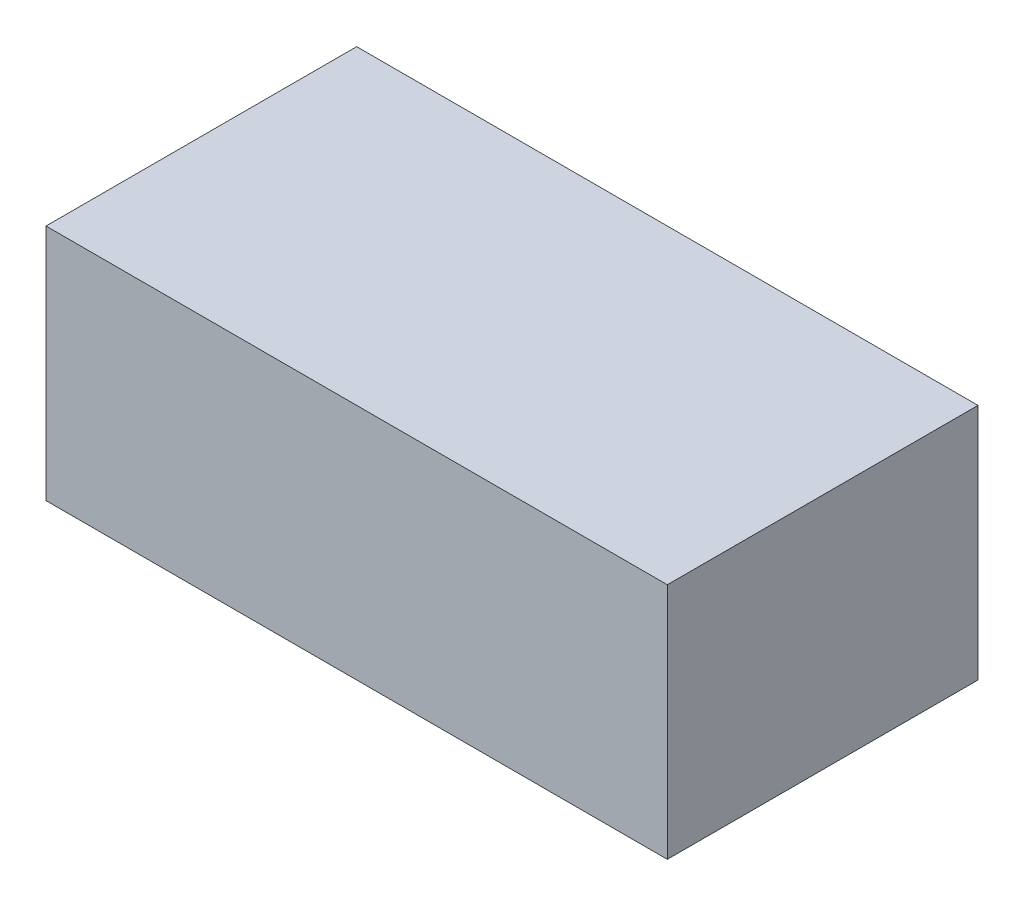
SolidWorks part; units mm, degrees
ref_plane "Front Plane" through (0, 0, 0) normal (0, 0, 1) x (1, 0, 0)
ref_plane "Top Plane" through (0, 0, 0) normal (0, 1, 0) x (1, 0, 0)
ref_plane "Right Plane" through (0, 0, 0) normal (1, 0, 0) x (0, 0, -1)
sketch "Sketch4" plane through (0, 0, 0) normal (0, 1, 0) x (1, 0, 0)
  line L1 (-145, 72.5) -> (145, 72.5)
  line L2 (-145, 72.5) -> (-145, -72.5)
  line L3 (-145, -72.5) -> (145, -72.5)
  line L4 (145, 72.5) -> (145, -72.5)
  line L5 (-145, 72.5) -> (145, -72.5) construction
  line L6 (-145, -72.5) -> (145, 72.5) construction
  point P0 (0, 0)
  dimension "D1" = 145
  dimension "D2" = 290
extrude "Boss-Extrude3" add sketch "Sketch4" along normal blind 111
sketch "Sketch5" plane through (0, 0, 0) normal (0, 1, 0) x (1, 0, 0)
  line L0 (-145, 72.5) -> (-145, -72.5) construction
  line L1 (-143, 70.5) -> (143, 70.5)
  line L2 (-143, 70.5) -> (-143, -70.5)
  line L3 (-143, -70.5) -> (143, -70.5)
  line L4 (143, 70.5) -> (143, -70.5)
  line L5 (145, 72.5) -> (-145, 72.5) construction
  line L6 (-145, -72.5) -> (145, -72.5) construction
  line L7 (145, -72.5) -> (145, 72.5) construction
  dimension "D1" = 2
  dimension "D2" = 2
  dimension "D3" = 2
  dimension "D4" = 2
extrude "Cut-Extrude2" cut sketch "Sketch5" along normal blind 110.8
